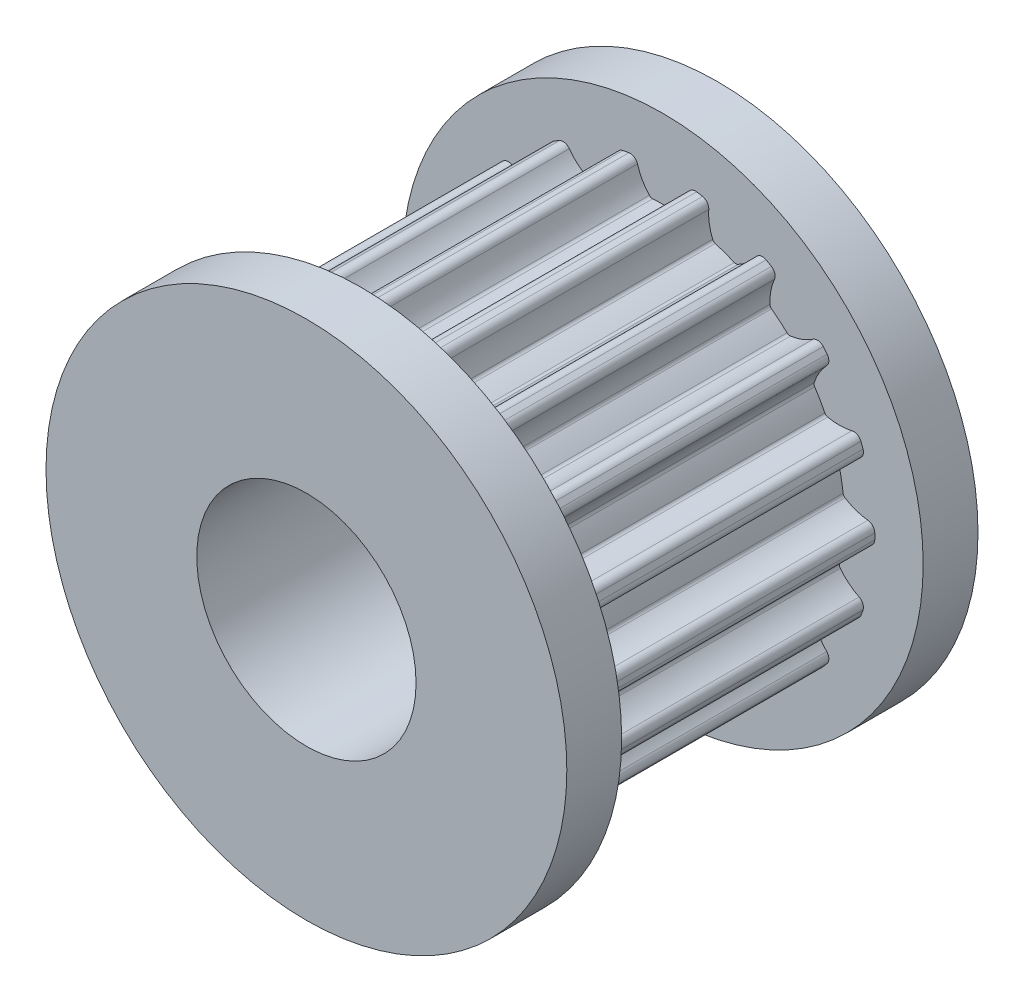
SolidWorks part; units mm, degrees
material "6061-T6 (SS)"
ref_plane "前基準面" through (0, 0, 0) normal (0, 0, 1) x (1, 0, 0)
ref_plane "上基準面" through (0, 0, 0) normal (0, 1, 0) x (1, 0, 0)
ref_plane "右基準面" through (0, 0, 0) normal (1, 0, 0) x (0, 0, -1)
sketch "草圖1" plane through (0, 0, 0) normal (0, 0, 1) x (1, 0, 0)
  circle A0 centre (0, 0) radius 7.735
  dimension "D1" = 15.47
extrude "填料-伸長1" add sketch "草圖1" along normal mid plane 11
sketch "草圖2" plane through (0, 0, 5.5) normal (0, 0, 1) x (1, 0, 0)
  line L0 (0, 0) -> (0, 7.735) construction
  line L1 (0, 7.735) -> (0, 7.989) construction
  line L2 (-0.975, 7.989) -> (0.975, 7.989) construction
  circle A0 centre (0, 0) radius 7.735 construction
  arc A1 (-0.3698, 6.6147) -> (0.3698, 6.6147) centre (0, 0) cw
  arc A2 (-0.3698, 6.6147) -> (-0.4894, 6.6638) centre (-0.3782, 6.7644) cw
  arc A3 (-0.4894, 6.6638) -> (-0.9214, 7.4375) centre (0.975, 7.989) cw
  arc A4 (-1.235, 7.6358) -> (-0.9214, 7.4375) centre (-1.1903, 7.3594) cw
  arc A5 (0.3698, 6.6147) -> (0.4894, 6.6638) centre (0.3782, 6.7644) ccw
  arc A6 (0.4894, 6.6638) -> (0.9214, 7.4375) centre (-0.975, 7.989) ccw
  arc A7 (1.235, 7.6358) -> (0.9214, 7.4375) centre (1.1903, 7.3594) ccw
  arc A8 (-1.235, 7.6358) -> (1.235, 7.6358) centre (0, 0) cw
  dimension "D1" = 0.15
  dimension "D2" = 1.975
  dimension "D3" = 0.28
  dimension "D4" = 1.11
  dimension "D5" = 0.254
  dimension "D6" = 1.95
extrude "除料-伸長1" cut sketch "草圖2" against normal through all and the other way through all
pattern_circular "環狀複製排列1" count 18 over 360 about axis through (0, 0, 0) along (0, 0, 1) of "除料-伸長1"
sketch "草圖3" plane through (0, 0, 5.5) normal (0, 0, 1) x (1, 0, 0)
  circle A0 centre (0, 0) radius 9.5
  dimension "D1" = 19
extrude "填料-伸長2" add sketch "草圖3" along normal blind 2
sketch "草圖9" plane through (0, 0, -5.5) normal (0, 0, -1) x (-1, 0, 0)
  circle A0 centre (0, 0) radius 9.5
  circle A1 centre (0, 0) radius 9.5 construction
extrude "填料-伸長3" add sketch "草圖9" along normal blind 2
sketch "草圖4" plane through (0, 0, 7.5) normal (0, 0, 1) x (1, 0, 0)
  circle A0 centre (0, 0) radius 4
  dimension "D1" = 8
extrude "除料-伸長2" cut sketch "草圖4" against normal through all
sketch "草圖10" plane through (0, 0, 0) normal (0, 1, 0) x (1, 0, 0)
  circle A0 centre (0, 0) radius 2
  dimension "D1" = 4
extrude "除料-伸長3" cut sketch "草圖10" against normal through all
sketch "草圖11" plane through (0, 0, 0) normal (1, 0, 0) x (0, 0, -1)
  circle A0 centre (0, 0) radius 2
  dimension "D1" = 4
extrude "除料-伸長4" cut sketch "草圖11" against normal through all
